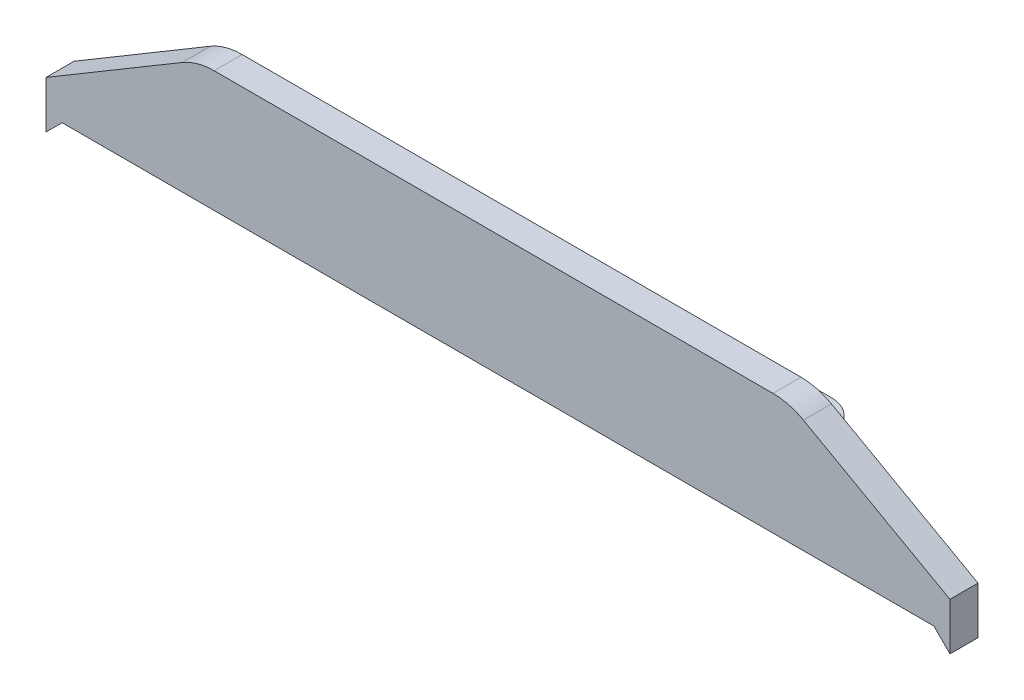
SolidWorks part; units mm, degrees
ref_plane "Front Plane" through (0, 0, 0) normal (0, 0, 1) x (1, 0, 0)
ref_plane "Top Plane" through (0, 0, 0) normal (0, 1, 0) x (1, 0, 0)
ref_plane "Right Plane" through (0, 0, 0) normal (1, 0, 0) x (0, 0, -1)
sketch "Sketch1" plane through (0, 0, 0) normal (0, 0, 1) x (1, 0, 0)
  line L0 (119.2183, -36.3858) -> (104.2183, -36.3858)
  line L1 (145, -58.3858) -> (0, -58.3858)
  line L2 (145, -58.3858) -> (145, -50.8)
  line L3 (145, -50.8) -> (0, -50.8)
  line L4 (0, -58.3858) -> (0, -50.8)
  line L5 (79.2183, -36.3858) -> (64.2183, -36.3858)
  line L6 (79.2183, -36.3858) -> (79.2183, -58.3858)
  line L8 (145, -50.8) -> (123.7883, -50.8)
  line L9 (123.7883, -50.8) -> (123.7883, -53.8)
  line L10 (123.7883, -53.8) -> (21.2117, -53.8)
  line L11 (21.2117, -53.8) -> (21.2117, -50.8)
  line L12 (21.2117, -50.8) -> (0, -50.8)
  line L13 (0, -50.8) -> (0, -58.3858)
  line L14 (2.5858, -55.8) -> (142.4142, -55.8)
  line L15 (0, -50.8) -> (0, -58.3858)
  line L16 (145, -50.8) -> (123.7883, -50.8)
  line L17 (123.7883, -50.8) -> (123.7883, -53.8)
  line L18 (123.7883, -53.8) -> (21.2117, -53.8)
  line L19 (21.2117, -53.8) -> (21.2117, -50.8)
  line L20 (21.2117, -50.8) -> (0, -50.8)
  line L24 (64.2183, -36.3858) -> (64.2183, -58.3858)
  line L25 (119.2183, -36.3858) -> (119.2183, -58.3858)
  line L26 (104.2183, -36.3858) -> (104.2183, -58.3858)
  line L27 (39.2183, -36.3858) -> (24.2183, -36.3858)
  line L28 (39.2183, -36.3858) -> (39.2183, -58.3858)
  line L29 (24.2183, -36.3858) -> (24.2183, -58.3858)
  line L30 (104.2183, -36.3858) -> (39.2183, -36.3858)
  line L31 (145, -50.8) -> (119.2183, -36.3858)
  line L32 (24.2183, -36.3858) -> (0, -50.8)
  line L46 (145, -58.3858) -> (145, -50.8)
  line L47 (145, -58.3858) -> (145, -50.8)
  line L100 (2.5858, -55.8) -> (142.4142, -55.8)
  line L101 (142.4142, -55.8) -> (145, -58.3858)
  line L102 (142.4142, -55.8) -> (145, -58.3858)
  line L103 (0, -58.3858) -> (2.5858, -55.8)
  line L104 (0, -58.3858) -> (2.5858, -55.8)
  point P6 (71.7183, -38.3858)
  dimension "D2" = 20
  dimension "D3" = 15
  dimension "D4" = 22
  dimension "D1" = 0
  dimension "D5" = 2
  dimension "D6" = 2
extrude "Boss-Extrude1" add sketch "Sketch1" along normal blind 4.5
sketch "Sketch2" plane through (0, -53.8, 0) normal (0, 1, 0) x (1, 0, 0)
  line L0 (123.5054, 0) -> (110.9064, 12.599)
  line L1 (107.5123, 14.0049) -> (37.4877, 14.0049)
  line L2 (34.0936, 12.599) -> (21.4946, 0)
  line L4 (107.5123, 14.2049) -> (37.4877, 14.2049)
  line L5 (33.9522, 12.7405) -> (21.2117, 0)
  line L6 (21.2117, 0) -> (123.7883, 0)
  line L7 (123.7883, 0) -> (111.0478, 12.7405)
  line L10 (21.4946, 0) -> (123.5054, 0)
  circle A0 centre (37.4877, 9.2049) radius 1.65 construction
  circle A1 centre (107.5123, 9.2049) radius 1.65 construction
  arc A2 (37.4877, 14.2049) -> (33.9522, 12.7405) centre (37.4877, 9.2049) ccw
  arc A3 (111.0478, 12.7405) -> (107.5123, 14.2049) centre (107.5123, 9.2049) ccw
  circle A6 centre (37.4877, 9.2049) radius 1.65
  circle A7 centre (107.5123, 9.2049) radius 1.65
  arc A8 (110.9064, 12.599) -> (107.5123, 14.0049) centre (107.5123, 9.2049) ccw
  arc A9 (37.4877, 14.0049) -> (34.0936, 12.599) centre (37.4877, 9.2049) ccw
  dimension "D1" = 0
extrude "Boss-Extrude2" add sketch "Sketch2" along normal up to surface (3 mm away)
fillet "Fillet1" radius 10 2 edges at (24.2183, -36.3858, 2.25) (119.2183, -36.3858, 2.25)
